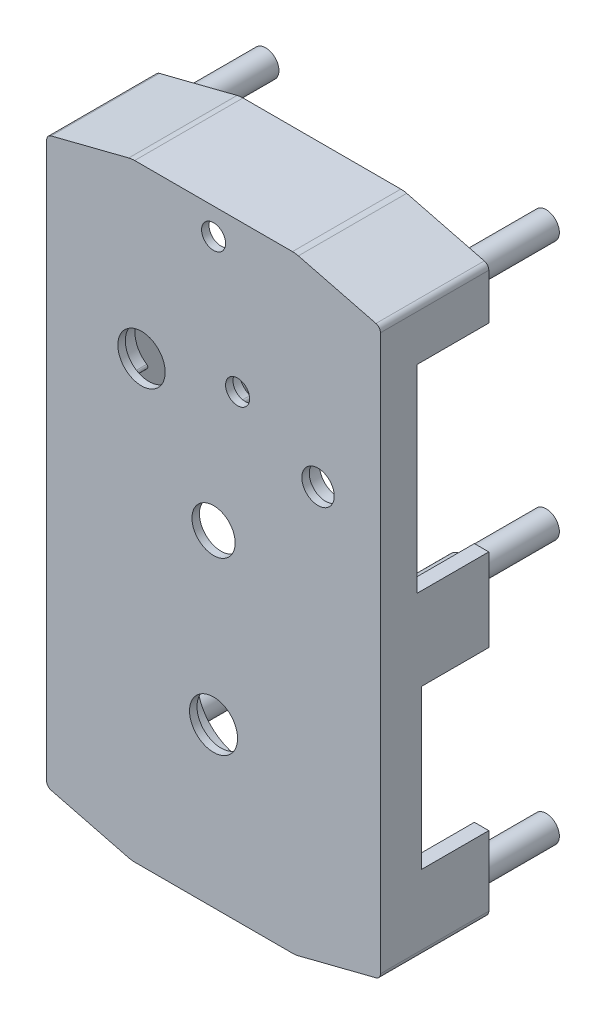
SolidWorks part; units mm, degrees
material "Polybutadiene (PB)"
ref_plane "Front Plane" through (0, 0, 0) normal (0, 0, 1) x (1, 0, 0)
ref_plane "Top Plane" through (0, 0, 0) normal (0, 1, 0) x (1, 0, 0)
ref_plane "Right Plane" through (0, 0, 0) normal (1, 0, 0) x (0, 0, -1)
sketch "Sketch2" plane through (0, 0, 0) normal (0, 0, 1) x (1, 0, 0)
  line L0 (0, 25.3) -> (0, 27.2341) construction
  line L1 (-3.6651, 0) -> (-10.2349, 0)
  line L2 (0, 1.0944) -> (0, 24.2056)
  line L3 (-3.6651, 25.3) -> (-10.2349, 25.3)
  line L4 (-13.9, 1.0944) -> (-13.9, 24.2056)
  line L5 (-3.54, 25.3) -> (-3.54, 27.2341) construction
  line L6 (-13.9, 24.2056) -> (-13.9, 27.2341) construction
  line L7 (-10.36, 25.3) -> (-10.36, 27.2341) construction
  line L8 (-13.9, 24.4) -> (13.315, 24.4) construction
  line L9 (-13.7116, 24.4479) -> (-10.4813, 25.2692)
  line L10 (-3.4187, 25.2692) -> (-0.1884, 24.4479)
  line L11 (-10.36, 27.2341) -> (-3.54, 27.2341) construction
  line L12 (-6.95, 27.2341) -> (-6.95, 25.3) construction
  line L13 (-0.1884, 24.4479) -> (-3.4187, 25.2692)
  line L14 (-10.2349, 0) -> (-6.95, 0) construction
  line L15 (-6.95, 0) -> (-6.95, 25.3) construction
  line L16 (-6.95, 12.65) -> (0, 12.65) construction
  line L17 (-3.4187, 0.0308) -> (-0.1884, 0.8521)
  line L18 (-3.6651, 0) -> (-10.2349, 0)
  line L19 (-13.7116, 0.8521) -> (-10.4813, 0.0308)
  line L20 (0, 1.0944) -> (0, 0) construction
  line L21 (-13.9, 24.2056) -> (-13.9, 25.2692) construction
  line L22 (-10.2349, 0) -> (-13.9, 0) construction
  arc A0 (-10.2349, 25.3) -> (-10.4813, 25.2692) centre (-10.2349, 24.3) ccw
  arc A1 (-13.7116, 24.4479) -> (-13.9, 24.2056) centre (-13.65, 24.2056) ccw
  arc A2 (-3.6651, 25.3) -> (-3.4187, 25.2692) centre (-3.6651, 24.3) cw
  arc A3 (-0.1884, 24.4479) -> (0, 24.2056) centre (-0.25, 24.2056) cw
  arc A4 (-0.1884, 0.8521) -> (0, 1.0944) centre (-0.25, 1.0944) ccw
  arc A5 (-3.6651, 0) -> (-3.4187, 0.0308) centre (-3.6651, 1) ccw
  arc A6 (-10.2349, 0) -> (-10.4813, 0.0308) centre (-10.2349, 1) cw
  arc A7 (-13.7116, 0.8521) -> (-13.9, 1.0944) centre (-13.65, 1.0944) cw
  dimension "D2" = 1
  dimension "D6" = 0.25
  dimension "D3" = 13.9
  dimension "D4" = 3.54
  dimension "D5" = 0.9
  dimension "D7" = 25.3
  dimension "D8" = 24.2056
  dimension "D9" = 24.4479
  dimension "D10" = 1.9341
extrude "Boss-Extrude1" add sketch "Sketch2" along normal blind 4.51 contours A7 L19 A6 L1 A5 L17 A4 L2 A3 L10 A2 L3 A0 L9 A1 L4
sketch "Sketch4" plane through (0, 0, 0) normal (0, 0, -1) x (-1, 0, 0)
  line L37 (13.3, 1.3665) -> (13.3, 23.9335)
  line L38 (13.3, 23.9335) -> (10.3334, 24.6877)
  line L39 (10.2349, 24.7) -> (3.6651, 24.7)
  line L40 (3.5666, 24.6877) -> (0.6, 23.9335)
  line L41 (0.6, 23.9335) -> (0.6, 1.3665)
  line L42 (0.6, 1.3665) -> (3.5666, 0.6123)
  line L43 (3.6651, 0.6) -> (10.2349, 0.6)
  line L44 (10.3334, 0.6123) -> (13.3, 1.3665)
  line L45 (13.3, 1.3665) -> (13.3, 23.9335)
  line L46 (13.3, 23.9335) -> (10.3334, 24.6877)
  line L47 (10.2349, 24.7) -> (3.6651, 24.7)
  line L48 (3.5666, 24.6877) -> (0.6, 23.9335)
  line L49 (0.6, 23.9335) -> (0.6, 1.3665)
  line L50 (0.6, 1.3665) -> (3.5666, 0.6123)
  line L51 (3.6651, 0.6) -> (10.2349, 0.6)
  line L52 (10.3334, 0.6123) -> (13.3, 1.3665)
  arc A31 (10.3334, 24.6877) -> (10.2349, 24.7) centre (10.2349, 24.3) ccw
  arc A32 (3.6651, 24.7) -> (3.5666, 24.6877) centre (3.6651, 24.3) ccw
  arc A33 (3.5666, 0.6123) -> (3.6651, 0.6) centre (3.6651, 1) ccw
  arc A34 (10.2349, 0.6) -> (10.3334, 0.6123) centre (10.2349, 1) ccw
  arc A35 (10.3334, 24.6877) -> (10.2349, 24.7) centre (10.2349, 24.3) ccw
  arc A36 (3.6651, 24.7) -> (3.5666, 24.6877) centre (3.6651, 24.3) ccw
  arc A37 (3.5666, 0.6123) -> (3.6651, 0.6) centre (3.6651, 1) ccw
  arc A38 (10.2349, 0.6) -> (10.3334, 0.6123) centre (10.2349, 1) ccw
  dimension "D1" = 0.6
extrude "Cut-Extrude1" cut sketch "Sketch4" against normal blind 4.2
sketch "Sketch5" plane through (0, 0, 4.2) normal (0, 0, -1) x (-1, 0, 0)
  line L0 (6.95, 0.6) -> (6.95, 6.6) construction
  line L1 (3.6651, 0.6) -> (10.2349, 0.6) construction
  circle A0 centre (6.95, 6.6) radius 1
  dimension "D2" = 2
  dimension "D1" = 6
extrude "Cut-Extrude2" cut sketch "Sketch5" against normal blind 4.1
sketch "Sketch6" plane through (0, 0, 4.2) normal (0, 0, -1) x (-1, 0, 0)
  line L0 (0, 1.0944) -> (0, 24.2056) construction
  line L1 (7.0866, 4.1037) -> (9.7174, 0.6)
  line L2 (6.2586, 4.1975) -> (3.5666, 0.6123)
  line L3 (6.8134, 4.1037) -> (4.1826, 0.6)
  line L4 (3.6651, 0.6) -> (10.2349, 0.6) construction
  line L5 (6.95, 6.6) -> (6.95, 0.6) construction
  line L6 (7.6414, 4.1975) -> (10.3334, 0.6123)
  line L7 (4.4762, 6.9612) -> (0.6, 8.3665)
  line L8 (0.6, 23.9335) -> (0.6, 1.3665) construction
  line L9 (4.5985, 7.4487) -> (0.6, 8.8984)
  line L10 (9.3015, 7.4487) -> (13.3, 8.8984)
  line L11 (9.4238, 6.9612) -> (13.3, 8.3665)
  circle A0 centre (6.95, 6.6) radius 2.5
  circle A1 centre (6.95, 6.6) radius 2
  dimension "D1" = 5
  dimension "D2" = 0.5
  dimension "D3" = 0.5
  dimension "D4" = 4.1826
  dimension "D5" = 0.5
  dimension "D6" = 7
  dimension "D7" = 6.3612
extrude "Boss-Extrude2" add sketch "Sketch6" along normal blind 1
sketch "Sketch7" plane through (0, 0, 4.2) normal (0, 0, -1) x (-1, 0, 0)
  line L0 (6.95, 6.6) -> (6.95, 13.6) construction
  circle A0 centre (6.95, 13.6) radius 0.9
  dimension "D2" = 1.8
  dimension "D1" = 7
extrude "Cut-Extrude3" cut sketch "Sketch7" against normal blind 1
sketch "Sketch8" plane through (0, 0, 4.2) normal (0, 0, -1) x (-1, 0, 0)
  line L0 (6.95, 24.7) -> (6.95, 18.7833) construction
  line L1 (10.2349, 24.7) -> (3.6651, 24.7) construction
  circle A0 centre (6.95, 24.2) radius 0.5
  dimension "D1" = 1
extrude "Cut-Extrude4" cut sketch "Sketch8" against normal blind 1
sketch "Sketch9" plane through (0, 0, 4.2) normal (0, 0, -1) x (-1, 0, 0)
  line L0 (6.95, 13.6) -> (6.95, 19.1) construction
  line L1 (6.95, 19.1) -> (5.95, 19.1) construction
  line L2 (6.95, 18.3) -> (9.95, 18.3) construction
  line L3 (6.95, 17.35) -> (2.6, 17.35) construction
  circle A0 centre (5.95, 19.1) radius 0.5
  circle A1 centre (9.95, 18.3) radius 0.985
  circle A2 centre (2.6, 17.35) radius 0.675
  dimension "D3" = 1
  dimension "D6" = 1.97
  dimension "D9" = 1.35
  dimension "D1" = 5.5
  dimension "D2" = 1
  dimension "D4" = 3
  dimension "D5" = 4.7
  dimension "D7" = 3.75
  dimension "D8" = 4.35
extrude "Cut-Extrude5" cut sketch "Sketch9" against normal blind 1
sketch "Sketch10" plane through (0, 0, 4.2) normal (0, 0, -1) x (-1, 0, 0)
  line L0 (6.95, 24.7) -> (3.6651, 24.7) construction
  arc A0 (5.5102, 18.3436) -> (6.2986, 18.2974) centre (5.95, 19.1) cw construction
  arc A1 (6.3484, 18.1828) -> (5.4473, 18.2355) centre (5.95, 19.1) ccw
  arc A2 (6.2488, 18.4121) -> (5.573, 18.4516) centre (5.95, 19.1) ccw
  arc A3 (6.2488, 18.4121) -> (6.3484, 18.1828) centre (6.2986, 18.2974) ccw
  arc A4 (5.4473, 18.2355) -> (5.573, 18.4516) centre (5.5102, 18.3436) ccw
  circle A5 centre (2.6, 17.35) radius 0.9
  circle A6 centre (2.6, 17.35) radius 0.75
  arc A7 (8.8672, 18.7756) -> (10.5981, 17.3108) centre (9.95, 18.3) cw construction
  arc A8 (10.6529, 17.2271) -> (8.7757, 18.8159) centre (9.95, 18.3) ccw
  arc A9 (10.5433, 17.3944) -> (8.9588, 18.7354) centre (9.95, 18.3) ccw
  arc A10 (10.5433, 17.3944) -> (10.6529, 17.2271) centre (10.5981, 17.3108) ccw
  arc A11 (8.7757, 18.8159) -> (8.9588, 18.7354) centre (8.8672, 18.7756) ccw
  point P4 (6.0011, 19.9735)
  point P22 (10.714, 19.2027)
  dimension "D1" = 0.25
  dimension "D2" = 1
  dimension "D5" = 1.8
  dimension "D7" = 0.2
  dimension "D10" = 1.2826
  dimension "D3" = 0.377
  dimension "D4" = 0.2988
  dimension "D8" = 0.9912
  dimension "D9" = 0.5933
  dimension "D6" = 0.15
extrude "Boss-Extrude3" add sketch "Sketch10" along normal blind 0.5
sketch "Sketch11" plane through (0, 0, 0) normal (1, 0, 0) x (0, 0, -1)
  line L0 (0, 22.3) -> (-3, 22.3) construction
  line L1 (0, 1.0944) -> (0, 24.2056) construction
  line L3 (0, 25.3) -> (-3.683, 25.3) construction
  line L4 (0, 25.3) -> (0, 27.2341) construction
  line L5 (0, 22.3) -> (-3, 22.3)
  line L6 (-3, 22.3) -> (-3, 14.05)
  line L7 (-3, 14.05) -> (0, 14.05)
  line L8 (0, 1.0944) -> (0, 24.2056) construction
  line L9 (0, 0) -> (-3, 0) construction
  line L10 (0, 4) -> (-2.8, 4) construction
  line L11 (0, 4) -> (-2.8, 4)
  line L12 (-2.8, 4) -> (-2.8, 10.6)
  line L13 (-2.8, 10.6) -> (0, 10.6)
  line L14 (0, 22.3) -> (0, 14.05)
  line L15 (0, 10.6) -> (0, 4)
  dimension "D1" = 3
  dimension "D2" = 3
  dimension "D3" = 8.25
  dimension "D4" = 4
  dimension "D5" = 2.8
  dimension "D6" = 6.6
extrude "Cut-Extrude6" cut sketch "Sketch11" against normal blind 0.6
sketch "Sketch12" plane through (0, 0, 0) normal (0, -1, 0) x (1, 0, 0)
  line L0 (-3.7, 0) -> (-3.7, 3.8719) construction
  line L1 (-3.6651, 0) -> (-10.2349, 0) construction
  line L2 (0, 0) -> (0, 4.2505) construction
  line L3 (-3.7, 0) -> (-3.7, 2.5)
  line L4 (-3.7, 2.5) -> (-10.2, 2.5)
  line L5 (-10.2, 2.5) -> (-10.2, 0)
  line L7 (-3.7, 0) -> (-10.2, 0)
  dimension "D1" = 3.7
  dimension "D2" = 2.5
  dimension "D3" = 6.5
extrude "Cut-Extrude7" cut sketch "Sketch12" against normal blind 0.6
sketch "Sketch13" plane through (0, 25.3, 0) normal (0, 1, 0) x (1, 0, 0)
sketch "Sketch15" plane through (-13.9, 0, 0) normal (-1, 0, 0) x (0, 0, 1)
  line L0 (0, 0) -> (2.8745, 0) construction
  line L1 (0, 4) -> (2.5, 4) construction
  line L2 (0, 1.0944) -> (0, 24.2056) construction
  line L3 (0, 4) -> (2.5, 4)
  line L4 (2.5, 4) -> (2.5, 10.6)
  line L5 (2.5, 10.6) -> (0, 10.6)
  line L6 (0, 10.6) -> (0, 4)
  line L7 (0, 18) -> (2, 18) construction
  line L8 (0, 18) -> (2, 18)
  line L9 (2, 18) -> (2, 22)
  line L10 (2, 22) -> (0, 22)
  line L11 (0, 1.0944) -> (0, 24.2056) construction
  line L12 (0, 18) -> (0, 22)
  dimension "D1" = 4
  dimension "D2" = 2.5
  dimension "D3" = 6.6
  dimension "D4" = 7.4
  dimension "D5" = 2
  dimension "D6" = 4
extrude "Cut-Extrude8" cut sketch "Sketch15" against normal blind 0.6
sketch "Sketch16" plane through (0, 0, 4.2) normal (0, 0, -1) x (-1, 0, 0)
  line L0 (4.1826, 0.6) -> (9.7174, 0.6) construction
  line L1 (0.6, 23.9335) -> (0.6, 8.8984) construction
  line L2 (6.95, 24.7) -> (6.95, 0.6) construction
  line L3 (6.95, 0) -> (6.95, 25.3) construction
  circle A0 centre (1.1123, 23.5335) radius 0.65
  circle A1 centre (1.1123, 12.75) radius 0.65
  circle A2 centre (1.1123, 1.7665) radius 0.65
  circle A3 centre (12.7877, 1.7665) radius 0.65
  circle A4 centre (12.7877, 12.75) radius 0.65
  circle A5 centre (12.7877, 23.5335) radius 0.65
  dimension "D1" = 1.3
  dimension "D3" = 1.3
  dimension "D6" = 1.3
  dimension "D2" = 0.4
  dimension "D4" = 12.15
  dimension "D5" = 0.5123
  dimension "D7" = 0.4
extrude "Boss-Extrude4" add sketch "Sketch16" along normal blind 4.2
sketch "Sketch17" plane through (0, 0, 0) normal (0, 0, -1) x (-1, 0, 0)
  line L0 (6.95, 25.3) -> (6.95, 0) construction
  line L1 (3.6651, 25.3) -> (10.2349, 25.3) construction
  circle A0 centre (1.1123, 12.75) radius 0.55
  circle A1 centre (1.1123, 23.5335) radius 0.55
  circle A2 centre (1.1123, 1.7665) radius 0.55
  circle A3 centre (12.7877, 1.7665) radius 0.55
  circle A4 centre (12.7877, 12.75) radius 0.55
  circle A5 centre (12.7877, 23.5335) radius 0.55
  dimension "D1" = 1.1
  dimension "D2" = 1.1
  dimension "D3" = 1.1
extrude "Boss-Extrude5" add sketch "Sketch17" along normal blind 3.5
